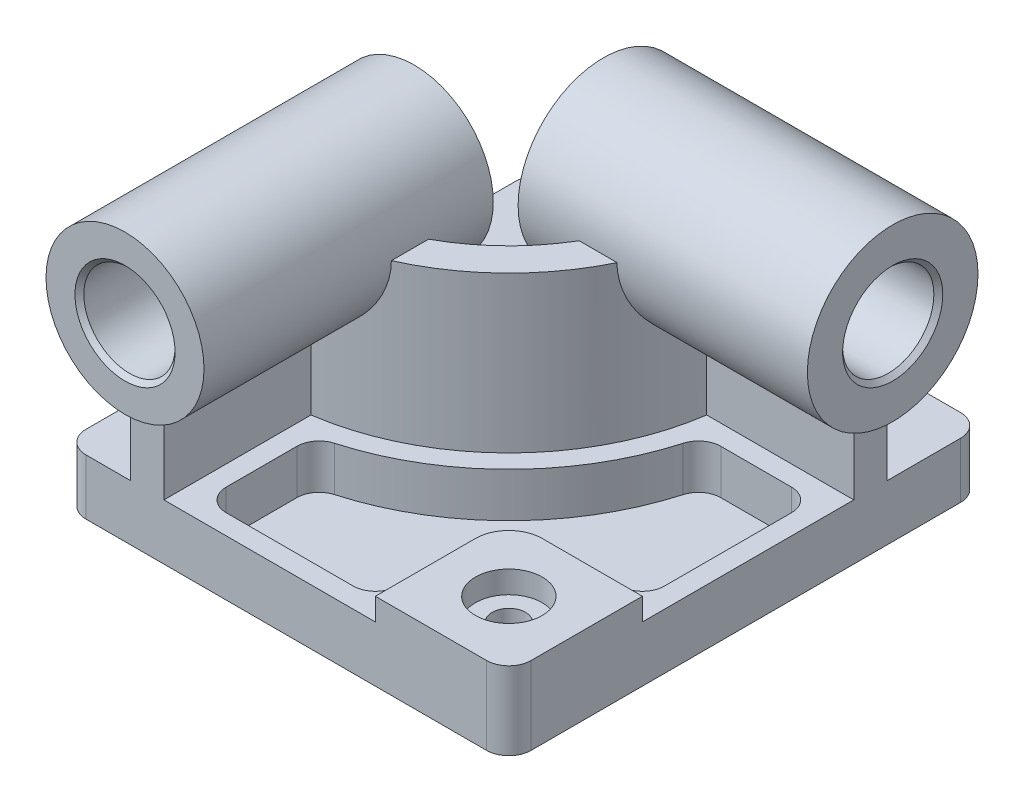
SolidWorks part; units mm, degrees
material "Alloy Steel"
ref_plane "정면" through (0, 0, 0) normal (0, 0, 1) x (1, 0, 0)
ref_plane "평면" through (0, 0, 0) normal (0, 1, 0) x (1, 0, 0)
ref_plane "우측면" through (0, 0, 0) normal (1, 0, 0) x (0, 0, -1)
sketch "스케치1" plane through (0, 0, 0) normal (0, 1, 0) x (1, 0, 0)
  line L1 (10, 0) -> (190, 0)
  line L2 (0, 10) -> (0, 203)
  line L3 (10, 213) -> (190, 213)
  line L4 (200, 10) -> (200, 203)
  arc A0 (0, 10) -> (10, 0) centre (10, 10) ccw
  arc A1 (190, 0) -> (200, 10) centre (190, 10) ccw
  arc A2 (200, 203) -> (190, 213) centre (190, 203) ccw
  arc A3 (0, 203) -> (10, 213) centre (10, 203) cw
  point P7 (0, 0)
  point P12 (200, 213)
  point P15 (0, 213)
  dimension "D3" = 10
  dimension "D1" = 213
  dimension "D2" = 200
extrude "보스-돌출1" add sketch "스케치1" along normal blind 25
sketch "스케치2" plane through (0, 25, 0) normal (0, 1, 0) x (1, 0, 0)
  line L4 (10, 0) -> (190, 0) construction
  line L5 (200, 10) -> (200, 203) construction
  line L6 (140, 0) -> (190, 0)
  line L7 (200, 10) -> (200, 60)
  line L8 (140, 0) -> (140, 45)
  line L9 (155, 60) -> (200, 60)
  line L10 (140, 10) -> (140, 203) construction
  line L11 (10, 60) -> (190, 60) construction
  line L12 (200, 10) -> (200, 203) construction
  line L13 (10, 0) -> (190, 0) construction
  arc A0 (190, 0) -> (200, 10) centre (190, 10) ccw construction
  arc A1 (190, 0) -> (200, 10) centre (190, 10) ccw
  arc A2 (155, 60) -> (140, 45) centre (155, 45) ccw
  dimension "D1" = 15
  dimension "D2" = 60
  dimension "D3" = 60
extrude "보스-돌출2" add sketch "스케치2" along normal blind 10
sketch "스케치3" plane through (0, 35, 0) normal (0, 1, 0) x (1, 0, 0)
  line L0 (140, 0) -> (170, 0) construction
  line L1 (170, 0) -> (170, 30) construction
hole_wizard "M8 육각 머리 볼트용 카운터보어1" positions "3D스케치1" profile "스케치4" counterbore size "M8" standard "Ansi Metric" end condition through all
sketch3d "3D스케치1"
  point P0 (170, 35, -30)
sketch "스케치4" plane through (170, 35, -30) normal (1, 0, 0) x (0, 0, 1)
  line L0 (0, 0) -> (0, 35)
  line L1 (0, 35) -> (7.5, 35)
  line L3 (7.5, 35) -> (7.5, 10)
  line L4 (7.5, 10) -> (15, 10)
  line L5 (15, 10) -> (15, 0)
  line L7 (15, 0) -> (0, 0)
  line L11 (0, -6.35) -> (0, 107.95) construction
  dimension "관통 구멍 지름" = 15
  dimension "관통 구멍 깊이" = 35
  dimension "카운터보어 지름" = 30
  dimension "카운터보어 깊이" = 10
sketch "스케치5" plane through (0, 25, 0) normal (0, 1, 0) x (1, 0, 0)
  line L0 (200, 60) -> (200, 203) construction
  line L1 (149.2476, 146) -> (181, 146)
  line L2 (140, 45) -> (140, 0) construction
  line L3 (191, 79) -> (191, 136)
  line L4 (10, 0) -> (140, 0) construction
  line L6 (181, 69) -> (155, 69)
  line L9 (131, 45) -> (131, 19)
  line L12 (64, 9) -> (121, 9)
  line L18 (54, 19) -> (54, 50.7524)
  arc A1 (191, 136) -> (181, 146) centre (181, 136) ccw
  arc A2 (191, 79) -> (181, 69) centre (181, 79) cw
  arc A3 (155, 69) -> (131, 45) centre (155, 45) ccw
  arc A4 (54, 19) -> (64, 9) centre (64, 19) ccw
  arc A5 (121, 9) -> (131, 19) centre (121, 19) ccw
  arc A6 (155, 60) -> (140, 45) centre (155, 45) ccw construction
  arc A8 (61.2581, 60.3691) -> (139.6309, 138.7419) centre (30, 170) ccw
  arc A10 (139.6309, 138.7419) -> (149.2476, 146) centre (149.2476, 136) cw
  arc A11 (54, 50.7524) -> (61.2581, 60.3691) centre (64, 50.7524) cw
  dimension "D1" = 9
  dimension "D3" = 9
  dimension "D4" = 9
  dimension "D7" = 10
  dimension "D8" = 10
  dimension "D9" = 9
  dimension "D10" = 24
  dimension "D11" = 114
  dimension "D12" = 170
  dimension "D2" = 9
  dimension "D5" = 77
  dimension "D6" = 77
  dimension "D13" = 170
extrude "컷-돌출1" cut sketch "스케치5" against normal blind 20
ref_plane "평면1" through (0, 0, 10) normal (0, 0, 1) x (1, 0, 0)
ref_plane "평면2" through (210, 0, 0) normal (1, 0, 0) x (0, 0, -1)
sketch "스케치6" plane through (0, 0, 10) normal (0, 0, 1) x (1, 0, 0)
  circle A0 centre (37.5, 95) radius 35.5
  dimension "D1" = 95
  dimension "D3" = 71
  dimension "D4" = 162.5
extrude "보스-돌출3" add sketch "스케치6" against normal blind 130 separate body
sketch "스케치7" plane through (210, 0, 0) normal (1, 0, 0) x (0, 0, -1)
  circle A1 centre (162.5, 95) radius 38.335
  dimension "D1" = 162.5
  dimension "D4" = 76.67
  dimension "D2" = 95
extrude "보스-돌출4" add sketch "스케치7" against normal blind 130 separate body
sketch "스케치8" plane through (0, 25, 0) normal (0, 1, 0) x (1, 0, 0)
  line L0 (10, 0) -> (140, 0) construction
  line L1 (200, 60) -> (200, 203) construction
  line L2 (30, 0) -> (45, 0)
  line L3 (200, 155) -> (133.923, 155)
  line L4 (200, 170) -> (120, 170)
  line L7 (30, 80) -> (30, 0)
  line L8 (181, 170) -> (149.2476, 170) construction
  line L9 (181, 155) -> (149.2476, 155) construction
  line L11 (200, 155) -> (200, 170)
  line L13 (45, 66.077) -> (45, 0)
  arc A1 (30, 80) -> (120, 170) centre (30, 170) ccw
  arc A2 (54.6774, 83.4493) -> (116.5507, 145.3226) centre (30, 170) ccw construction
  arc A3 (45, 66.077) -> (133.923, 155) centre (30, 170) ccw
  arc A4 (58.7903, 69.0242) -> (130.9758, 141.2097) centre (30, 170) ccw construction
  point P6 (67.5738, -2.887)
  point P7 (61.6877, 176.5757)
  dimension "D6" = 90
  dimension "D7" = 15
  dimension "D1" = 30
  dimension "D2" = 15
  dimension "D3" = 80
  dimension "D4" = 80
  dimension "D5" = 15
  dimension "D8" = 170
extrude "보스-돌출8" add sketch "스케치8" along normal blind 70
sketch "스케치9" plane through (0, 0, 10) normal (0, 0, 1) x (1, 0, 0)
  circle A0 centre (37.5, 95) radius 20.5
  dimension "D1" = 41
extrude "컷-돌출2" cut sketch "스케치9" against normal up to next
sketch "스케치10" plane through (210, 0, 0) normal (1, 0, 0) x (0, 0, -1)
  circle A0 centre (162.5, 95) radius 20.5
  dimension "D1" = 41
extrude "컷-돌출3" cut sketch "스케치10" against normal up to next
chamfer "모따기1" distance 2 angle 45 4 edges at (80, 95, -183) (58, 95, -120) (210, 95, -183) (58, 95, 10)
